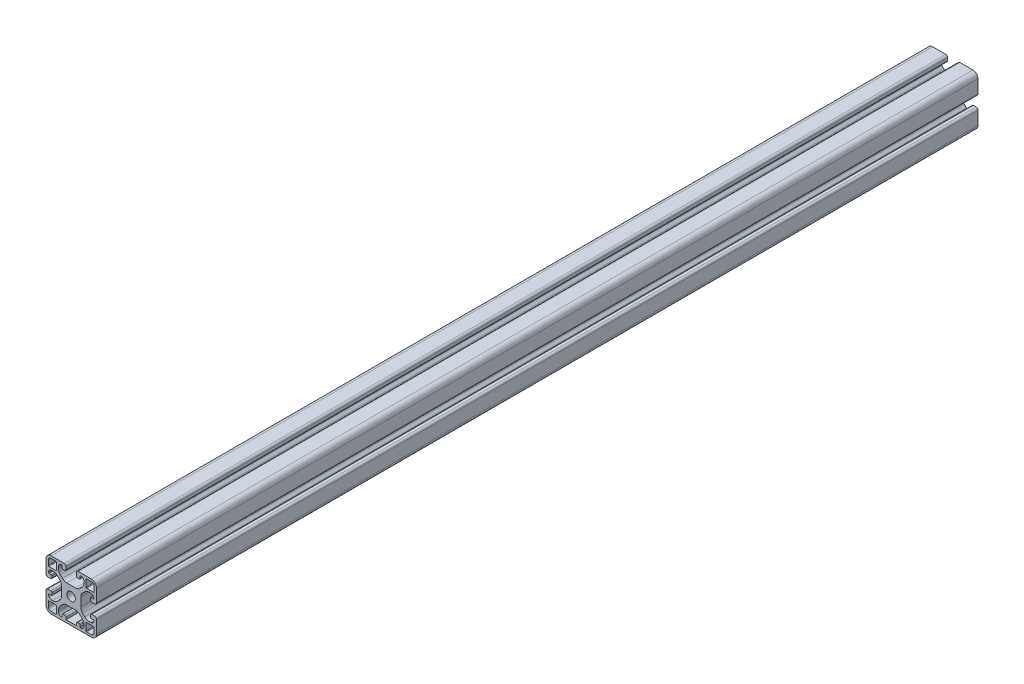
SolidWorks part; units mm, degrees
ref_plane "Ebene vorne" through (0, 0, 0) normal (0, 0, 1) x (1, 0, 0)
ref_plane "Ebene oben" through (0, 0, 0) normal (0, 1, 0) x (1, 0, 0)
ref_plane "Ebene rechts" through (0, 0, 0) normal (1, 0, 0) x (0, 0, -1)
ref_plane "Ebene1" through (0, 0, 1000) normal (0, 0, 1) x (1, 0, 0)
sketch "Skizze1" plane through (0, 0, 1000) normal (0, 0, 1) x (1, 0, 0)
  line L0 (27.8, 32.3) -> (27.8, 37.7)
  line L1 (28.3, 38.2) -> (32, 38.2)
  line L2 (34.2, 36) -> (34.2, 32.3)
  line L3 (33.7, 31.8) -> (28.3, 31.8)
  line L4 (28.3, 8.2) -> (33.7, 8.2)
  line L5 (34.2, 7.7) -> (34.2, 4)
  line L6 (32, 1.8) -> (28.3, 1.8)
  line L7 (27.8, 2.3) -> (27.8, 7.7)
  line L8 (3.7, 31.8) -> (-1.7, 31.8)
  line L9 (-2.2, 32.3) -> (-2.2, 36)
  line L10 (0, 38.2) -> (3.7, 38.2)
  line L11 (4.2, 37.7) -> (4.2, 32.3)
  line L12 (4.2, 7.7) -> (4.2, 2.3)
  line L13 (3.7, 1.8) -> (0, 1.8)
  line L14 (-2.2, 4) -> (-2.2, 7.7)
  line L15 (-1.7, 8.2) -> (3.7, 8.2)
  line L16 (20.1, 2) -> (11.9, 2)
  line L17 (11.9, 2) -> (11.9, 3.65)
  line L18 (10.9, 4.65) -> (9.4, 4.65)
  line L19 (8.9, 4.15) -> (8.9, 2.5)
  line L20 (5.9, 4.5) -> (5.9, 5.7076)
  line L21 (7.3645, 9.2431) -> (9.0569, 10.9355)
  line L22 (12.5924, 12.4) -> (19.4076, 12.4)
  line L23 (22.9431, 10.9355) -> (24.6355, 9.2431)
  line L24 (26.1, 5.7076) -> (26.1, 4.5)
  line L25 (23.1, 2.5) -> (23.1, 4.15)
  line L26 (22.6, 4.65) -> (21.1, 4.65)
  line L27 (20.1, 3.65) -> (20.1, 2)
  line L28 (5.9, 34.2924) -> (5.9, 35.5)
  line L29 (8.9, 37.5) -> (8.9, 35.85)
  line L30 (9.4, 35.35) -> (10.9, 35.35)
  line L31 (11.9, 36.35) -> (11.9, 38.5)
  line L32 (10.4, 40) -> (0, 40)
  line L33 (-4, 36) -> (-4, 25.6)
  line L34 (-2.5, 24.1) -> (-0.35, 24.1)
  line L35 (0.65, 25.1) -> (0.65, 26.6)
  line L36 (0.15, 27.1) -> (-1.5, 27.1)
  line L37 (0.5, 30.1) -> (1.7076, 30.1)
  line L38 (5.2431, 28.6355) -> (6.9355, 26.9431)
  line L39 (8.4, 23.4076) -> (8.4, 16.5924)
  line L40 (6.9355, 13.0569) -> (5.2431, 11.3645)
  line L41 (1.7076, 9.9) -> (0.5, 9.9)
  line L42 (-1.5, 12.9) -> (0.15, 12.9)
  line L43 (0.65, 13.4) -> (0.65, 14.9)
  line L44 (-0.35, 15.9) -> (-2.5, 15.9)
  line L45 (-4, 14.4) -> (-4, 4)
  line L46 (0, 0) -> (32, 0)
  line L47 (36, 4) -> (36, 14.4)
  line L48 (34.5, 15.9) -> (32.35, 15.9)
  line L49 (31.35, 14.9) -> (31.35, 13.4)
  line L50 (31.85, 12.9) -> (33.5, 12.9)
  line L51 (31.5, 9.9) -> (30.2924, 9.9)
  line L52 (26.7569, 11.3645) -> (25.0645, 13.0569)
  line L53 (23.6, 16.5924) -> (23.6, 23.4076)
  line L54 (25.0645, 26.9431) -> (26.7569, 28.6355)
  line L55 (30.2924, 30.1) -> (31.5, 30.1)
  line L56 (33.5, 27.1) -> (31.85, 27.1)
  line L57 (31.35, 26.6) -> (31.35, 25.1)
  line L58 (32.35, 24.1) -> (34.5, 24.1)
  line L59 (36, 25.6) -> (36, 36)
  line L60 (32, 40) -> (21.6, 40)
  line L61 (20.1, 38.5) -> (20.1, 36.35)
  line L62 (21.1, 35.35) -> (22.6, 35.35)
  line L63 (23.1, 35.85) -> (23.1, 37.5)
  line L64 (26.1, 35.5) -> (26.1, 34.2924)
  line L65 (24.6355, 30.7569) -> (22.9431, 29.0645)
  line L66 (19.4076, 27.6) -> (12.5924, 27.6)
  line L67 (9.0569, 29.0645) -> (7.3645, 30.7569)
  circle A0 centre (16, 20) radius 3.35
  arc A1 (28.3, 31.8) -> (27.8, 32.3) centre (28.3, 32.3) cw
  arc A2 (27.8, 37.7) -> (28.3, 38.2) centre (28.3, 37.7) cw
  arc A3 (32, 38.2) -> (34.2, 36) centre (32, 36) cw
  arc A4 (34.2, 32.3) -> (33.7, 31.8) centre (33.7, 32.3) cw
  arc A5 (27.8, 7.7) -> (28.3, 8.2) centre (28.3, 7.7) cw
  arc A6 (33.7, 8.2) -> (34.2, 7.7) centre (33.7, 7.7) cw
  arc A7 (34.2, 4) -> (32, 1.8) centre (32, 4) cw
  arc A8 (28.3, 1.8) -> (27.8, 2.3) centre (28.3, 2.3) cw
  arc A9 (4.2, 32.3) -> (3.7, 31.8) centre (3.7, 32.3) cw
  arc A10 (-1.7, 31.8) -> (-2.2, 32.3) centre (-1.7, 32.3) cw
  arc A11 (-2.2, 36) -> (0, 38.2) centre (0, 36) cw
  arc A12 (3.7, 38.2) -> (4.2, 37.7) centre (3.7, 37.7) cw
  arc A13 (3.7, 8.2) -> (4.2, 7.7) centre (3.7, 7.7) cw
  arc A14 (4.2, 2.3) -> (3.7, 1.8) centre (3.7, 2.3) cw
  arc A15 (0, 1.8) -> (-2.2, 4) centre (0, 4) cw
  arc A16 (-2.2, 7.7) -> (-1.7, 8.2) centre (-1.7, 7.7) cw
  arc A17 (11.9, 3.65) -> (10.9, 4.65) centre (10.9, 3.65) ccw
  arc A18 (9.4, 4.65) -> (8.9, 4.15) centre (9.4, 4.15) ccw
  arc A19 (8.9, 2.5) -> (8.4, 2) centre (8.4, 2.5) cw
  arc A20 (8.4, 2) -> (5.9, 4.5) centre (8.4, 4.5) cw
  arc A21 (5.9, 5.7076) -> (7.3645, 9.2431) centre (10.9, 5.7076) cw
  arc A22 (9.0569, 10.9355) -> (12.5924, 12.4) centre (12.5924, 7.4) cw
  arc A23 (19.4076, 12.4) -> (22.9431, 10.9355) centre (19.4076, 7.4) cw
  arc A24 (24.6355, 9.2431) -> (26.1, 5.7076) centre (21.1, 5.7076) cw
  arc A25 (26.1, 4.5) -> (23.6, 2) centre (23.6, 4.5) cw
  arc A26 (23.6, 2) -> (23.1, 2.5) centre (23.6, 2.5) cw
  arc A27 (23.1, 4.15) -> (22.6, 4.65) centre (22.6, 4.15) ccw
  arc A28 (21.1, 4.65) -> (20.1, 3.65) centre (21.1, 3.65) ccw
  arc A29 (7.3645, 30.7569) -> (5.9, 34.2924) centre (10.9, 34.2924) cw
  arc A30 (5.9, 35.5) -> (8.4, 38) centre (8.4, 35.5) cw
  arc A31 (8.4, 38) -> (8.9, 37.5) centre (8.4, 37.5) cw
  arc A32 (8.9, 35.85) -> (9.4, 35.35) centre (9.4, 35.85) ccw
  arc A33 (10.9, 35.35) -> (11.9, 36.35) centre (10.9, 36.35) ccw
  arc A34 (11.9, 38.5) -> (10.4, 40) centre (10.4, 38.5) ccw
  arc A35 (0, 40) -> (-4, 36) centre (0, 36) ccw
  arc A36 (-4, 25.6) -> (-2.5, 24.1) centre (-2.5, 25.6) ccw
  arc A37 (-0.35, 24.1) -> (0.65, 25.1) centre (-0.35, 25.1) ccw
  arc A38 (0.65, 26.6) -> (0.15, 27.1) centre (0.15, 26.6) ccw
  arc A39 (-1.5, 27.1) -> (-2, 27.6) centre (-1.5, 27.6) cw
  arc A40 (-2, 27.6) -> (0.5, 30.1) centre (0.5, 27.6) cw
  arc A41 (1.7076, 30.1) -> (5.2431, 28.6355) centre (1.7076, 25.1) cw
  arc A42 (6.9355, 26.9431) -> (8.4, 23.4076) centre (3.4, 23.4076) cw
  arc A43 (8.4, 16.5924) -> (6.9355, 13.0569) centre (3.4, 16.5924) cw
  arc A44 (5.2431, 11.3645) -> (1.7076, 9.9) centre (1.7076, 14.9) cw
  arc A45 (0.5, 9.9) -> (-2, 12.4) centre (0.5, 12.4) cw
  arc A46 (-2, 12.4) -> (-1.5, 12.9) centre (-1.5, 12.4) cw
  arc A47 (0.15, 12.9) -> (0.65, 13.4) centre (0.15, 13.4) ccw
  arc A48 (0.65, 14.9) -> (-0.35, 15.9) centre (-0.35, 14.9) ccw
  arc A49 (-2.5, 15.9) -> (-4, 14.4) centre (-2.5, 14.4) ccw
  arc A50 (-4, 4) -> (0, 0) centre (0, 4) ccw
  arc A51 (32, 0) -> (36, 4) centre (32, 4) ccw
  arc A52 (36, 14.4) -> (34.5, 15.9) centre (34.5, 14.4) ccw
  arc A53 (32.35, 15.9) -> (31.35, 14.9) centre (32.35, 14.9) ccw
  arc A54 (31.35, 13.4) -> (31.85, 12.9) centre (31.85, 13.4) ccw
  arc A55 (33.5, 12.9) -> (34, 12.4) centre (33.5, 12.4) cw
  arc A56 (34, 12.4) -> (31.5, 9.9) centre (31.5, 12.4) cw
  arc A57 (30.2924, 9.9) -> (26.7569, 11.3645) centre (30.2924, 14.9) cw
  arc A58 (25.0645, 13.0569) -> (23.6, 16.5924) centre (28.6, 16.5924) cw
  arc A59 (23.6, 23.4076) -> (25.0645, 26.9431) centre (28.6, 23.4076) cw
  arc A60 (26.7569, 28.6355) -> (30.2924, 30.1) centre (30.2924, 25.1) cw
  arc A61 (31.5, 30.1) -> (34, 27.6) centre (31.5, 27.6) cw
  arc A62 (34, 27.6) -> (33.5, 27.1) centre (33.5, 27.6) cw
  arc A63 (31.85, 27.1) -> (31.35, 26.6) centre (31.85, 26.6) ccw
  arc A64 (31.35, 25.1) -> (32.35, 24.1) centre (32.35, 25.1) ccw
  arc A65 (34.5, 24.1) -> (36, 25.6) centre (34.5, 25.6) ccw
  arc A66 (36, 36) -> (32, 40) centre (32, 36) ccw
  arc A67 (21.6, 40) -> (20.1, 38.5) centre (21.6, 38.5) ccw
  arc A68 (20.1, 36.35) -> (21.1, 35.35) centre (21.1, 36.35) ccw
  arc A69 (22.6, 35.35) -> (23.1, 35.85) centre (22.6, 35.85) ccw
  arc A70 (23.1, 37.5) -> (23.6, 38) centre (23.6, 37.5) cw
  arc A71 (23.6, 38) -> (26.1, 35.5) centre (23.6, 35.5) cw
  arc A72 (26.1, 34.2924) -> (24.6355, 30.7569) centre (21.1, 34.2924) cw
  arc A73 (22.9431, 29.0645) -> (19.4076, 27.6) centre (19.4076, 32.6) cw
  arc A74 (12.5924, 27.6) -> (9.0569, 29.0645) centre (12.5924, 32.6) cw
extrude "Aufsatz-Linear austragen1" add sketch "Skizze1" against normal blind 700
